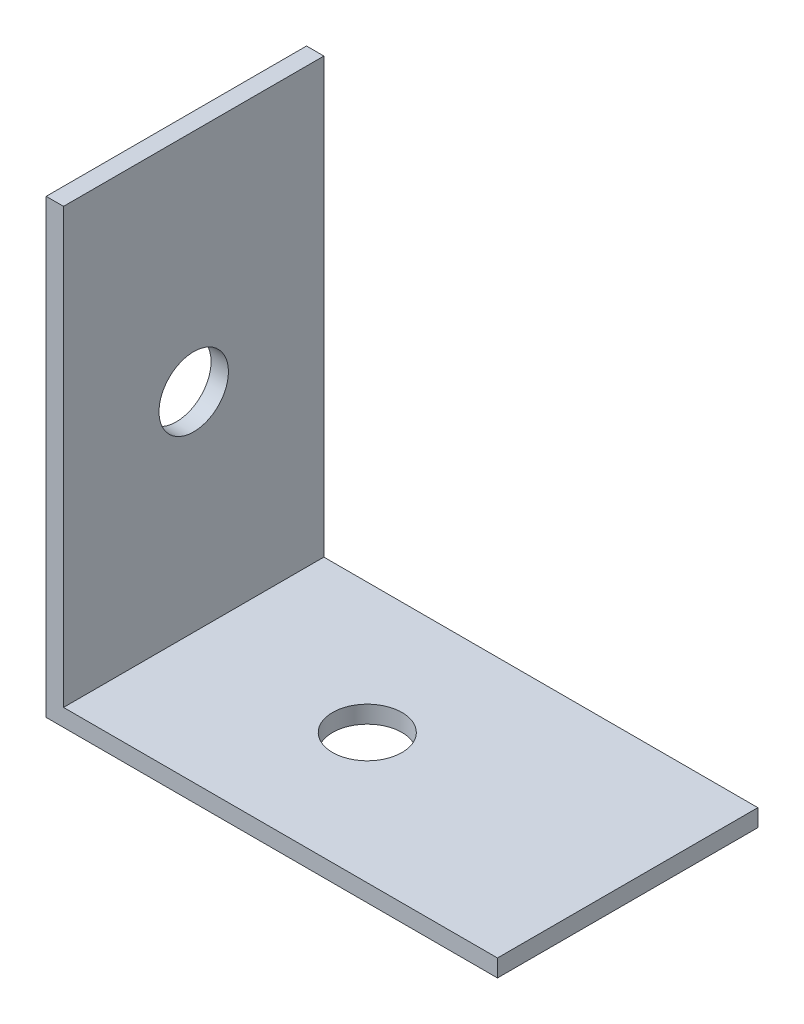
SolidWorks part; units mm, degrees
ref_plane "Plano frontal" through (0, 0, 0) normal (0, 0, 1) x (1, 0, 0)
ref_plane "Plano superior" through (0, 0, 0) normal (0, 1, 0) x (1, 0, 0)
ref_plane "Plano direito" through (0, 0, 0) normal (1, 0, 0) x (0, 0, -1)
sketch "Esboço1" plane through (0, 0, 0) normal (0, 0, 1) x (1, 0, 0)
  line L0 (0, 0) -> (25, 0)
  line L1 (0, 0) -> (0, 25)
  line L2 (-1, -1) -> (-1, 25)
  line L3 (-1, -1) -> (25, -1)
  line L4 (0, 25) -> (-1, 25)
  line L5 (25, 0) -> (25, -1)
  dimension "D1" = 25
  dimension "D2" = 1
extrude "Ressalto-extrusão1" add sketch "Esboço1" along normal blind 15
sketch "Esboço2" plane through (0, 0, 0) normal (1, 0, 0) x (0, 0, -1)
  line L0 (0, 12) -> (-15, 12) construction
  line L1 (0, 25) -> (0, -1) construction
  line L2 (-15, 25) -> (-15, -1) construction
  circle A0 centre (-7.5, 12) radius 2
extrude "Corte-extrusão1" cut sketch "Esboço2" against normal blind 15
sketch "Esboço3" plane through (0, 0, 0) normal (0, 1, 0) x (1, 0, 0)
  line L0 (10, 0) -> (10, -15) construction
  line L1 (25, 0) -> (0, 0) construction
  line L2 (25, -15) -> (0, -15) construction
  line L3 (-1, -15) -> (-1, 0) construction
  circle A0 centre (10, -7.5) radius 2
  dimension "D1" = 11
extrude "Corte-extrusão2" cut sketch "Esboço3" against normal blind 10
